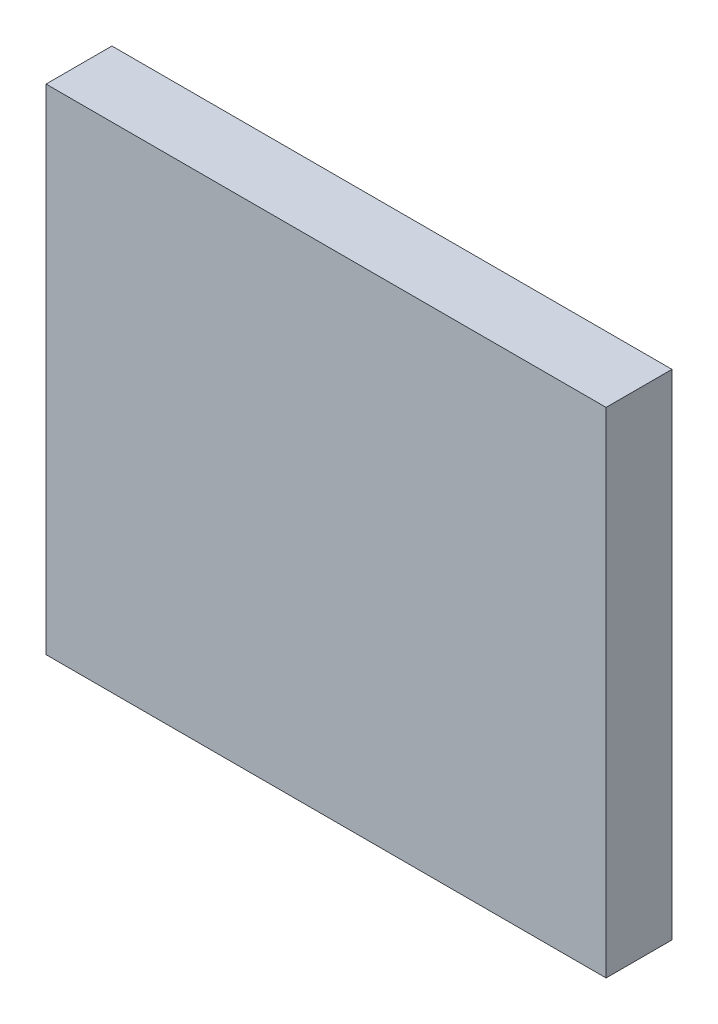
SolidWorks part; units mm, degrees
ref_plane "Front Plane" through (0, 0, 0) normal (0, 0, 1) x (1, 0, 0)
ref_plane "Top Plane" through (0, 0, 0) normal (0, 1, 0) x (1, 0, 0)
ref_plane "Right Plane" through (0, 0, 0) normal (1, 0, 0) x (0, 0, -1)
sketch "Sketch1" plane through (0, 0, 0) normal (0, 1, 0) x (1, 0, 0)
  line L1 (0, 0) -> (17, 0)
  line L2 (0, 0) -> (0, 2)
  line L3 (0, 2) -> (17, 2)
  line L4 (17, 0) -> (17, 2)
  dimension "D1" = 17
  dimension "D2" = 2
extrude "Boss-Extrude1" add sketch "Sketch1" along normal blind 15
